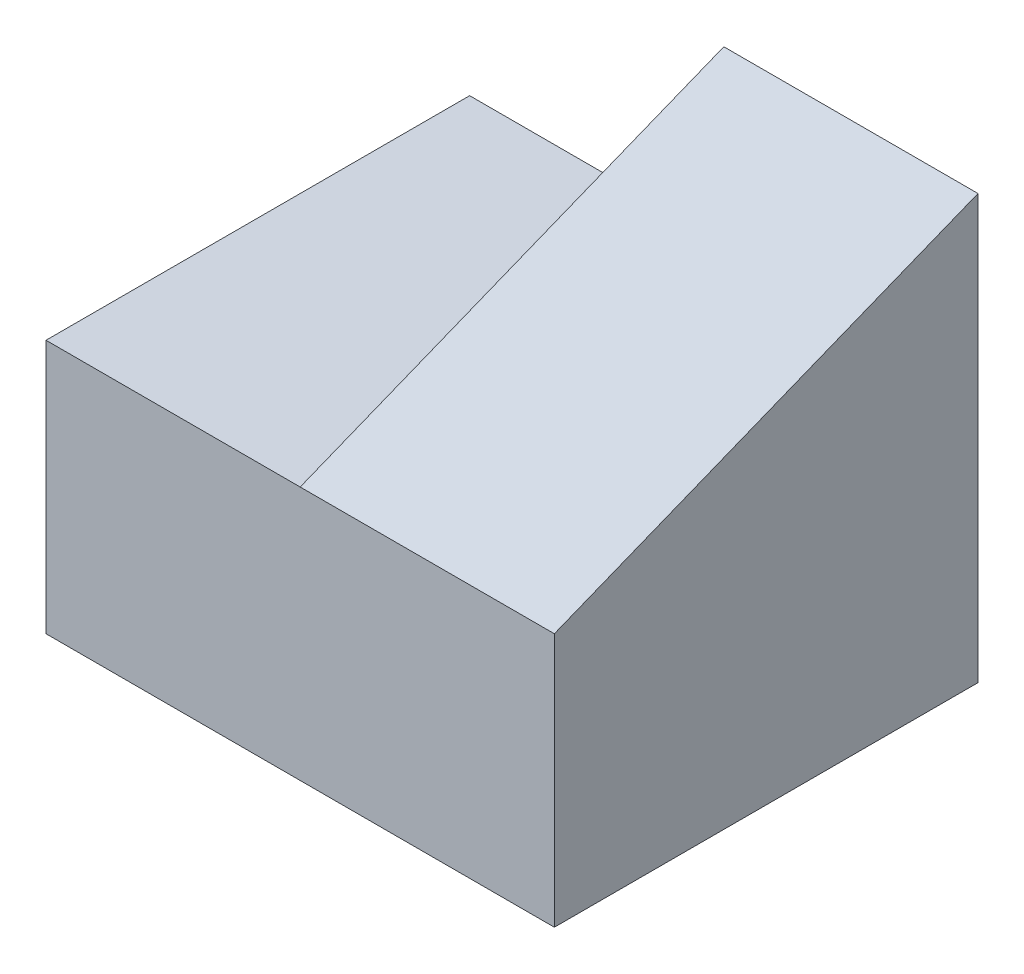
SolidWorks part; units mm, degrees
ref_plane "Front Plane" through (0, 0, 0) normal (0, 0, 1) x (1, 0, 0)
ref_plane "Top Plane" through (0, 0, 0) normal (0, 1, 0) x (1, 0, 0)
ref_plane "Right Plane" through (0, 0, 0) normal (1, 0, 0) x (0, 0, -1)
sketch "Sketch1" plane through (0, 0, 0) normal (0, 0, 1) x (1, 0, 0)
  line L1 (0, 0) -> (30, 0)
  line L2 (0, 0) -> (0, 15)
  line L3 (0, 15) -> (30, 15)
  line L4 (30, 0) -> (30, 15)
  dimension "D1" = 30
  dimension "D2" = 15
extrude "Boss-Extrude1" add sketch "Sketch1" along normal blind 25
sketch "Sketch2" plane through (30, 0, 0) normal (1, 0, 0) x (0, 0, -1)
  line L0 (0, 15) -> (0, 25)
  line L1 (0, 25) -> (-25, 15)
  line L2 (-25, 15) -> (0, 15)
  dimension "D1" = 10
extrude "Boss-Extrude2" add sketch "Sketch2" against normal blind 15
